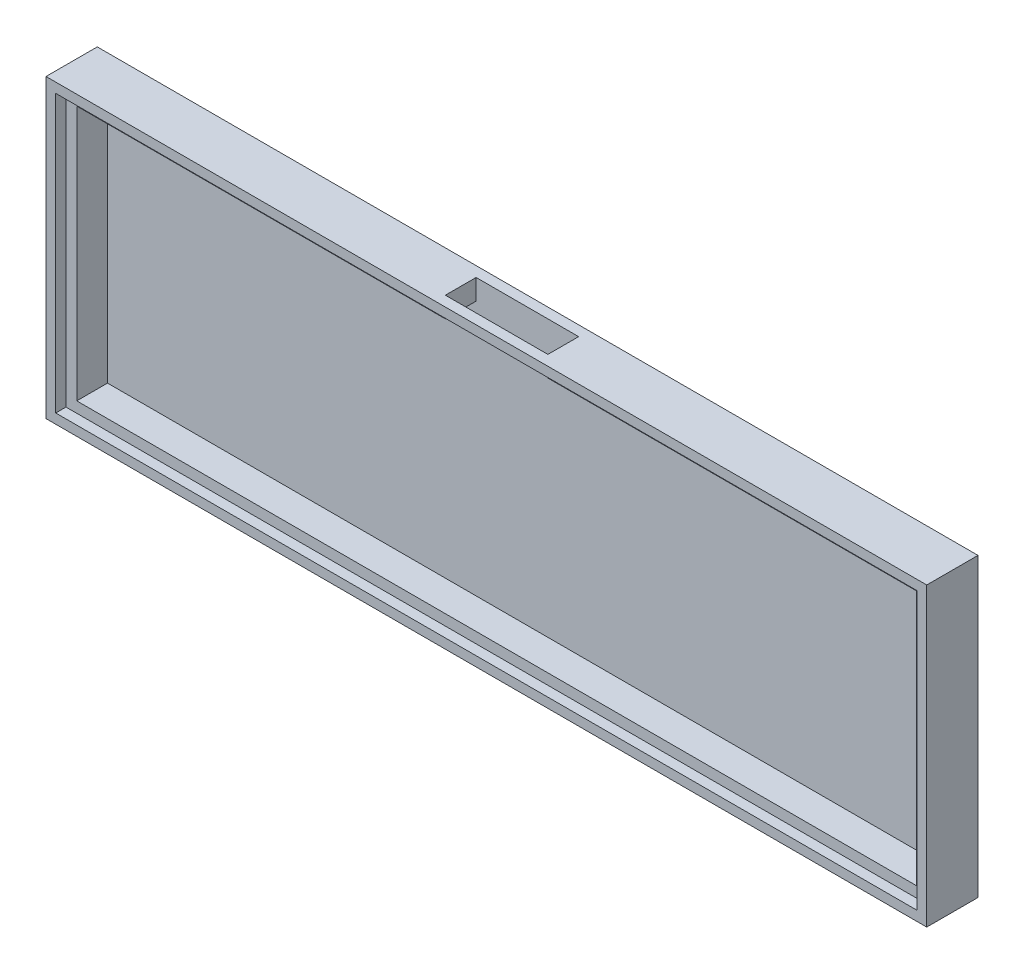
SolidWorks part; units mm, degrees
ref_plane "Front Plane" through (0, 0, 0) normal (0, 0, 1) x (1, 0, 0)
ref_plane "Top Plane" through (0, 0, 0) normal (0, 1, 0) x (1, 0, 0)
ref_plane "Right Plane" through (0, 0, 0) normal (1, 0, 0) x (0, 0, -1)
sketch "Sketch1" plane through (0, 0, 0) normal (0, 0, 1) x (1, 0, 0)
  line L1 (0, 0) -> (171.8, 0)
  line L2 (0, 0) -> (0, 57.8)
  line L3 (0, 57.8) -> (171.8, 57.8)
  line L4 (171.8, 0) -> (171.8, 57.8)
  dimension "D1" = 171.8
  dimension "D2" = 57.8
extrude "Main_Body" add sketch "Sketch1" along normal blind 10
sketch "Sketch2" plane through (0, 0, 10) normal (0, 0, 1) x (1, 0, 0)
  line L14 (4, 53.8) -> (4, 4)
  line L15 (4, 4) -> (167.8, 4)
  line L16 (167.8, 4) -> (167.8, 53.8)
  line L17 (167.8, 53.8) -> (4, 53.8)
  line L18 (4, 53.8) -> (4, 4)
  line L19 (4, 4) -> (167.8, 4)
  line L20 (167.8, 4) -> (167.8, 53.8)
  line L21 (167.8, 53.8) -> (4, 53.8)
  dimension "D1" = 4
extrude "Main_Cutout" cut sketch "Sketch2" against normal blind 8
sketch "Sketch3" plane through (53.8, 57.8, 0) normal (0, -1, 0) x (0, 0, 1)
  line L1 (10, -32.1) -> (0, -32.1) construction
  line L2 (10, -118) -> (10, 53.8) construction
  line L3 (0, -118) -> (0, 53.8) construction
  line L4 (2, -22.1) -> (8, -22.1)
  line L5 (2, -22.1) -> (2, -42.1)
  line L6 (2, -42.1) -> (8, -42.1)
  line L7 (8, -22.1) -> (8, -42.1)
  line L8 (5, -22.1) -> (5, -42.1) construction
  point P14 (5, -32.1)
  point P15 (5, -32.1)
  dimension "D1" = 6
  dimension "D2" = 20
extrude "Cable_Passthrough" cut sketch "Sketch3" along normal blind 4
sketch "Sketch9" plane through (0, 0, 10) normal (0, 0, 1) x (1, 0, 0)
  line L14 (169.9, 1.9) -> (169.9, 55.9)
  line L15 (1.9, 1.9) -> (169.9, 1.9)
  line L16 (1.9, 55.9) -> (1.9, 1.9)
  line L17 (169.9, 55.9) -> (1.9, 55.9)
  line L18 (169.9, 1.9) -> (169.9, 55.9)
  line L19 (1.9, 1.9) -> (169.9, 1.9)
  line L20 (1.9, 55.9) -> (1.9, 1.9)
  line L21 (169.9, 55.9) -> (1.9, 55.9)
  dimension "D1" = 1.9
extrude "Lid_Cutout" cut sketch "Sketch9" against normal blind 2
